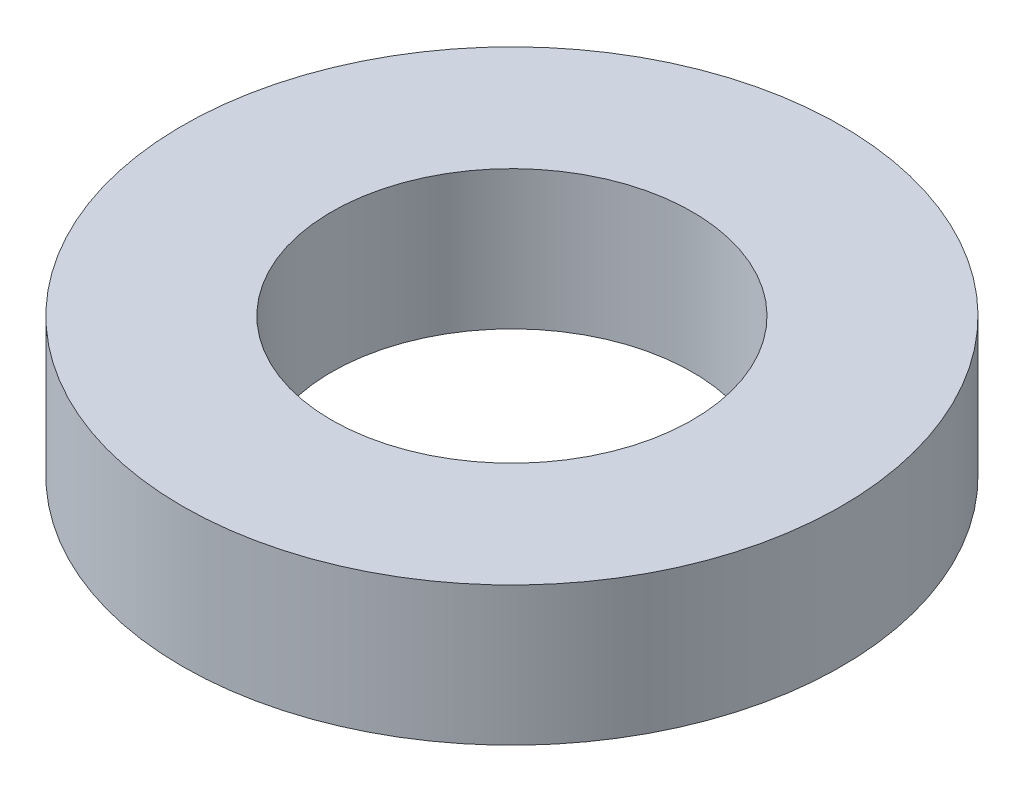
SolidWorks part; units mm, degrees
ref_plane "Front Plane" through (0, 0, 0) normal (0, 0, 1) x (1, 0, 0)
ref_plane "Top Plane" through (0, 0, 0) normal (0, 1, 0) x (1, 0, 0)
ref_plane "Right Plane" through (0, 0, 0) normal (1, 0, 0) x (0, 0, -1)
sketch "Sketch1" plane through (0, 0, 0) normal (0, 1, 0) x (1, 0, 0)
  circle A0 centre (0, 0) radius 4.75
  circle A1 centre (0, 0) radius 2.6
  dimension "D1" = 5.2
  dimension "D2" = 9.5
extrude "Boss-Extrude1" add sketch "Sketch1" along normal blind 2
move or copy body "Body-Move/Copy1" [suppressed] bodies to move or copy 101
